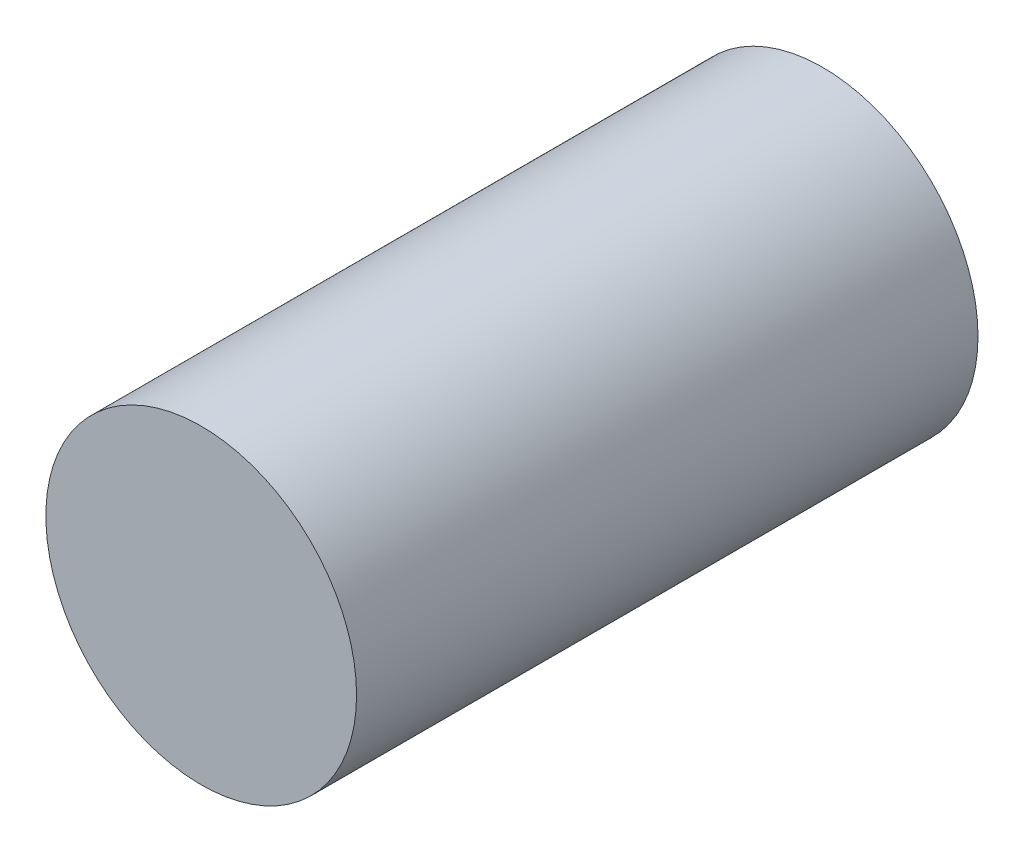
SolidWorks part; units mm, degrees
ref_plane "Front Plane" through (0, 0, 0) normal (0, 0, 1) x (1, 0, 0)
ref_plane "Top Plane" through (0, 0, 0) normal (0, 1, 0) x (1, 0, 0)
ref_plane "Right Plane" through (0, 0, 0) normal (1, 0, 0) x (0, 0, -1)
sketch "Sketch1" plane through (0, 0, 0) normal (0, 0, 1) x (1, 0, 0)
  circle A0 centre (0, 0) radius 5
  dimension "D1" = 10
extrude "Boss-Extrude1" add sketch "Sketch1" along normal blind 20 contours A0
